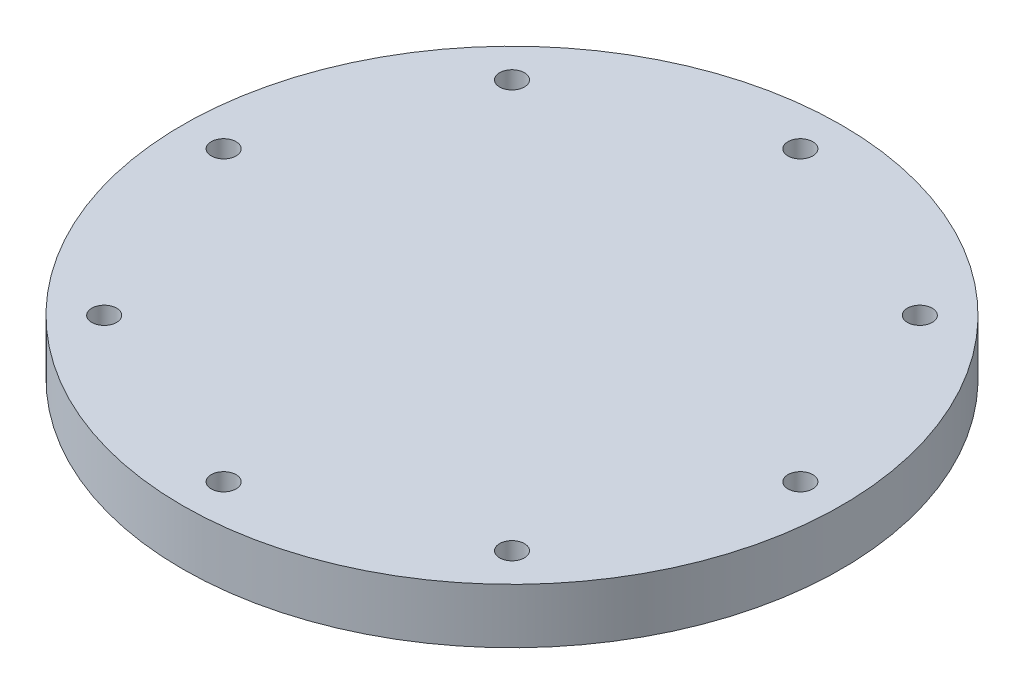
SolidWorks part; units mm, degrees
ref_plane "Front Plane" through (0, 0, 0) normal (0, 0, 1) x (1, 0, 0)
ref_plane "Top Plane" through (0, 0, 0) normal (0, 1, 0) x (1, 0, 0)
ref_plane "Right Plane" through (0, 0, 0) normal (1, 0, 0) x (0, 0, -1)
sketch "Sketch1" plane through (0, 0, 0) normal (0, 1, 0) x (1, 0, 0)
  circle A0 centre (0, 0) radius 38.1
  dimension "D1" = 76.2
extrude "Boss-Extrude1" add sketch "Sketch1" along normal blind 6.35
sketch "Sketch2" plane through (0, 0, 0) normal (0, -1, 0) x (1, 0, 0)
  circle A0 centre (0, 0) radius 33.3375
  circle A1 centre (0, 33.3375) radius 0.762
  dimension "D1" = 66.675
hole_wizard "CBORE for #4 Button Head Cap Screw1" positions "Sketch5" profile "Sketch4" counterbore size "#4" standard "ANSI Inch" end condition through all
sketch "Sketch5" plane through (0, 0, 0) normal (0, -1, 0) x (-1, 0, 0)
  point P0 (0, -33.3375)
sketch "Sketch4" plane through (0, 0, 33.3375) normal (1, 0, 0) x (0, 0, -1)
  line L0 (0, 0) -> (0, 6.35)
  line L1 (0, 6.35) -> (1.4351, 6.35)
  line L3 (1.4351, 6.35) -> (1.4351, 3.175)
  line L4 (1.4351, 3.175) -> (2.413, 3.175)
  line L5 (2.413, 3.175) -> (2.413, 0)
  line L7 (2.413, 0) -> (0, 0)
  line L11 (0, -6.35) -> (0, 107.95) construction
  dimension "Thru Hole Dia." = 2.8702
  dimension "Thru Hole Depth" = 6.35
  dimension "C'Bore Dia." = 4.826
  dimension "C'Bore Depth" = 3.175
pattern_circular "CirPattern1" count 8 over 360 about axis through (0, 0, 0) along (0, 1, 0) of "CBORE for #4 Button Head Cap Screw1"
